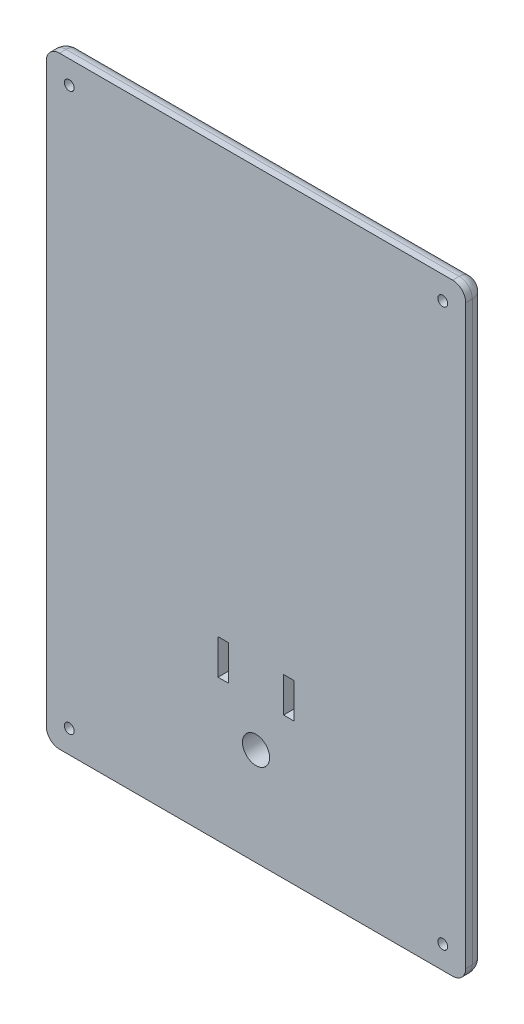
SolidWorks part; units mm, degrees
ref_plane "Front Plane" through (0, 0, 0) normal (0, 0, 1) x (1, 0, 0)
ref_plane "Top Plane" through (0, 0, 0) normal (0, 1, 0) x (1, 0, 0)
ref_plane "Right Plane" through (0, 0, 0) normal (1, 0, 0) x (0, 0, -1)
sketch "Sketch1" plane through (0, 0, 0) normal (0, 0, 1) x (1, 0, 0)
  line L0 (-40.64, -58.42) -> (40.64, -58.42)
  line L1 (-40.64, 58.42) -> (40.64, 58.42)
  line L2 (-40.64, 58.42) -> (-40.64, -58.42)
  line L3 (-40.64, -58.42) -> (40.64, -58.42) construction
  line L4 (40.64, 58.42) -> (40.64, -58.42)
  line L5 (-40.64, 58.42) -> (40.64, -58.42) construction
  line L6 (-40.64, -58.42) -> (40.64, 58.42) construction
  line L7 (-40.64, 58.42) -> (40.64, 58.42) construction
  line L9 (-40.64, 0) -> (40.64, 0) construction
  point P0 (0, 0)
extrude "Boss-Extrude1" add sketch "Sketch1" along normal blind 3.81 contours L1 L4 L0 L2
sketch "Sketch2" plane through (0, 0, 0) normal (0, 0, 1) x (1, 0, 0)
  line L1 (-29.6131, 7.3091) -> (8.4583, 7.3091)
  line L2 (-29.6131, 7.3091) -> (-29.6131, 1.7965)
  line L3 (-29.6131, 1.7965) -> (8.4583, 1.7965)
  line L4 (8.4583, 7.3091) -> (8.4583, 1.7965)
  line L5 (-29.6131, 0) -> (8.4583, 0)
  line L6 (-29.6131, 0) -> (-29.6131, -5.5047)
  line L7 (-29.6131, -5.5047) -> (8.4583, -5.5047)
  line L8 (8.4583, 0) -> (8.4583, -5.5047)
sketch "Sketch6" plane through (0, 0, 0) normal (0, 0, 1) x (1, 0, 0)
  line L0 (7.366, -27.559) -> (38.735, -27.559) construction
  line L1 (-7.366, -24.1554) -> (-5.334, -24.1554)
  line L2 (-7.366, -24.1554) -> (-7.366, -30.9626)
  line L3 (-7.366, -30.9626) -> (-5.334, -30.9626)
  line L4 (-5.334, -24.1554) -> (-5.334, -30.9626)
  line L5 (5.334, -24.1554) -> (7.366, -24.1554)
  line L6 (5.334, -24.1554) -> (5.334, -30.9626)
  line L7 (5.334, -30.9626) -> (7.366, -30.9626)
  line L8 (7.366, -24.1554) -> (7.366, -30.9626)
  line L10 (-7.366, -27.559) -> (-38.735, -27.559) construction
  line L13 (-36.195, -51.435) -> (36.195, -51.435) construction
  line L14 (-6.35, -24.1554) -> (-6.35, -30.9626) construction
  line L15 (6.35, -24.1554) -> (6.35, -30.9626) construction
  circle A0 centre (0, -39.497) radius 2.6289
  dimension "D4" = 5.2578
  dimension "D6" = 11.938
  dimension "D1" = 2.032
  dimension "D2" = 6.8072
  dimension "D3" = 12.7
  dimension "D5" = 11.938
sketch "Sketch7" plane through (0, 0, 0) normal (0, 0, 1) x (1, 0, 0)
  circle A0 centre (-36.195, 53.975) radius 0.9525
  circle A1 centre (-36.195, -53.975) radius 0.9525
  circle A2 centre (36.195, 53.975) radius 0.9525
  circle A3 centre (36.195, -53.975) radius 0.9525
  dimension "D1" = 1.905
extrude "Cut-Extrude5" cut sketch "Sketch6" along normal through all
extrude "Cut-Extrude6" cut sketch "Sketch7" along normal through all
fillet "Fillet1" radius 2.54 8 edges at (40.64, 0, 0) (0, -58.42, 0) (-40.64, 0, 0) (0, 58.42, 0) (40.64, 58.42, 1.905) (40.64, -58.42, 1.905) (-40.64, -58.42, 1.905) (-40.64, 58.42, 1.905)
chamfer "Chamfer1" distance 0.889 angle 45 4 edges at (-35.2425, 53.975, 0) (37.1475, 53.975, 0) (37.1475, -53.975, 0) (-35.2425, -53.975, 0)
extrude "Cut-Extrude7" cut sketch "Sketch2" along normal blind 1.27
ref_plane "Plane1" through (0, 0, 0) normal (0, 0, -1) x (-1, 0, 0)
sketch "Sketch10" plane through (0, 0, 0) normal (0, 0, -1) x (-1, 0, 0)
  text T0 "S/N:" font "Century Gothic" height in points 16
  text T1 "Firmware:" font "Century Gothic" height in points 16
extrude "Cut-Extrude8" cut sketch "Sketch10" against normal blind 1.905
